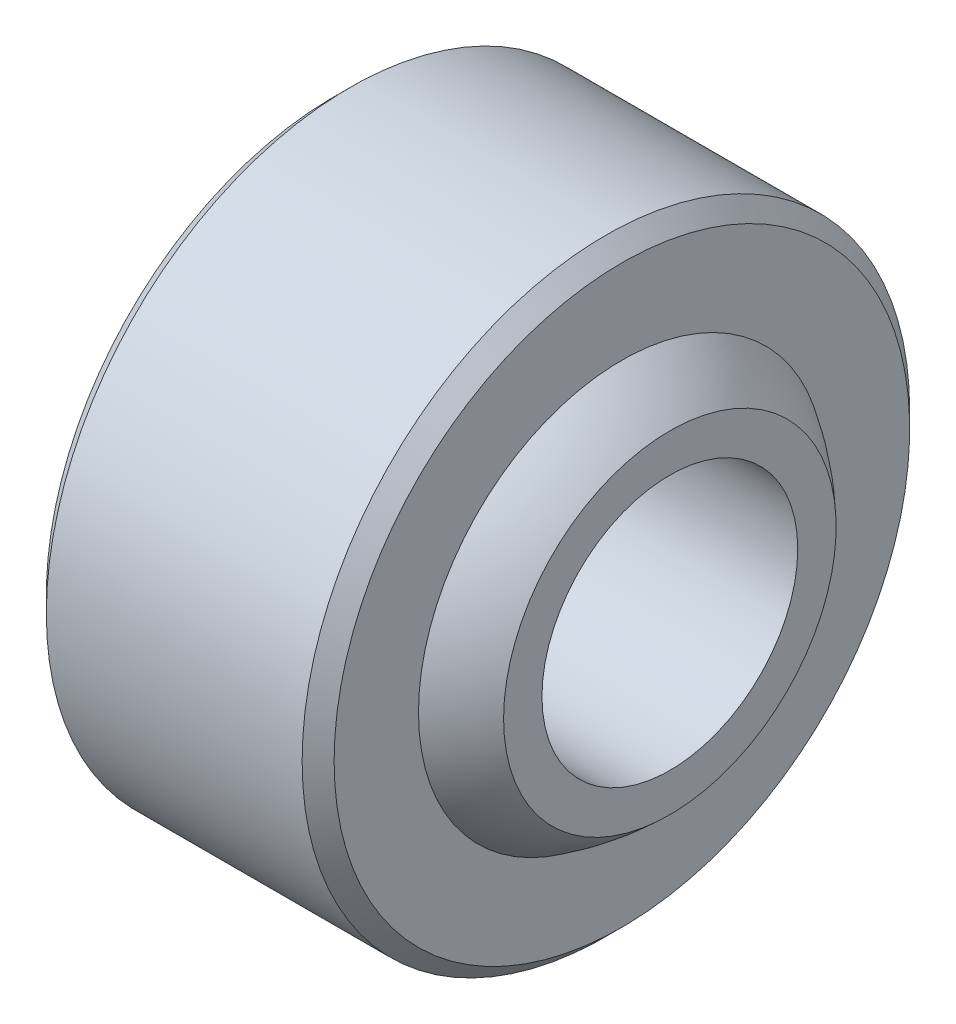
SolidWorks part; units mm, degrees
ref_plane "Płaszczyzna przednia" through (0, 0, 0) normal (0, 0, 1) x (1, 0, 0)
ref_plane "Płaszczyzna górna" through (0, 0, 0) normal (0, 1, 0) x (1, 0, 0)
ref_plane "Płaszczyzna prawa" through (0, 0, 0) normal (1, 0, 0) x (0, 0, -1)
sketch "Szkic1" plane through (0, 0, 0) normal (0, 0, 1) x (1, 0, 0)
  line L0 (-6, 0) -> (6, 0)
  line L1 (-6, 0) -> (-6, 1.2)
  line L2 (0, 0) -> (0, 5.5) construction
  line L3 (6, 0) -> (6, 1.2)
  line L5 (-4.5, 5.5) -> (4.5, 5.5)
  line L6 (-4.5, 5.5) -> (-4.5, 2.3614)
  line L7 (4.5, 5.5) -> (4.5, 2.3614)
  line L8 (-11.2613, -4) -> (19.1173, -4) construction
  arc A0 (6, 1.2) -> (4.5, 2.3614) centre (0, -5) ccw
  arc A2 (-4.5, 2.3614) -> (-6, 1.2) centre (0, -5) ccw
  dimension "D4" = 5.5
  dimension "D7" = 4
  dimension "D1" = 8.6279
  dimension "D2" = 6
  dimension "D3" = 9.5
  dimension "1,2" = 1.2
  dimension "D5" = 4.5
revolve "Obrót1" add sketch "Szkic1" angle 360 about L8
chamfer "Sfazowanie1" distance 0.5 angle 45 2 edges at (-4.5, -4, 9.5) (4.5, -4, 9.5)
